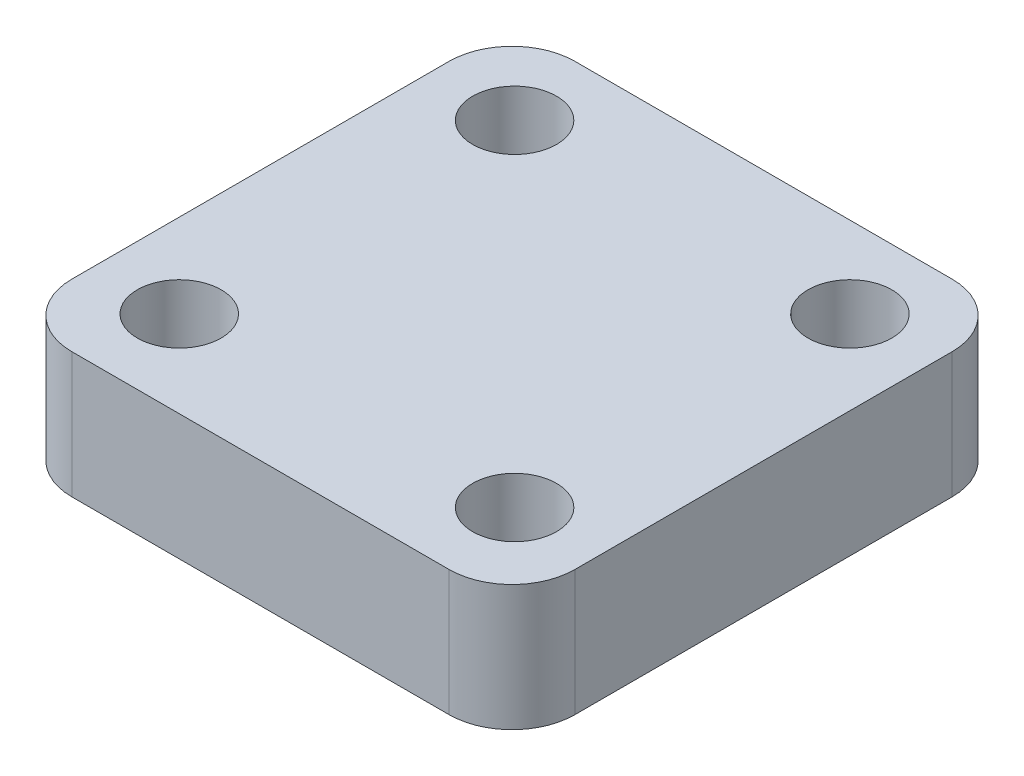
SolidWorks part; units mm, degrees
ref_plane "Front Plane" through (0, 0, 0) normal (0, 0, 1) x (1, 0, 0)
ref_plane "Top Plane" through (0, 0, 0) normal (0, 1, 0) x (1, 0, 0)
ref_plane "Right Plane" through (0, 0, 0) normal (1, 0, 0) x (0, 0, -1)
sketch "Çizim1" plane through (0, 0, 0) normal (0, 1, 0) x (1, 0, 0)
  line L1 (-450, 600) -> (450, 600)
  line L2 (-600, 450) -> (-600, -450)
  line L3 (-450, -600) -> (450, -600)
  line L4 (600, 450) -> (600, -450)
  arc A0 (600, 450) -> (450, 600) centre (450, 450) ccw
  arc A1 (600, -450) -> (450, -600) centre (450, -450) cw
  arc A2 (-600, -450) -> (-450, -600) centre (-450, -450) ccw
  arc A3 (-600, 450) -> (-450, 600) centre (-450, 450) cw
  circle A4 centre (-400, 406.1715) radius 100
  circle A5 centre (400, 406.1715) radius 100
  circle A6 centre (-400, -393.8285) radius 100
  circle A7 centre (400, -393.8285) radius 100
  point P7 (600, 600)
  point P12 (-600, -600)
  point P15 (-600, 600)
  point P24 (0, 0)
  point P25 (0, 0)
  dimension "D5" = 150
  dimension "D6" = 800
  dimension "D8" = 800
  dimension "D1" = 1200
  dimension "D2" = 1200
  dimension "D3" = 600
  dimension "D4" = 600
  dimension "D7" = 200
  dimension "D9" = 800
extrude "Yükseklik-Ekstrüzyon1" add sketch "Çizim1" along normal blind 300
